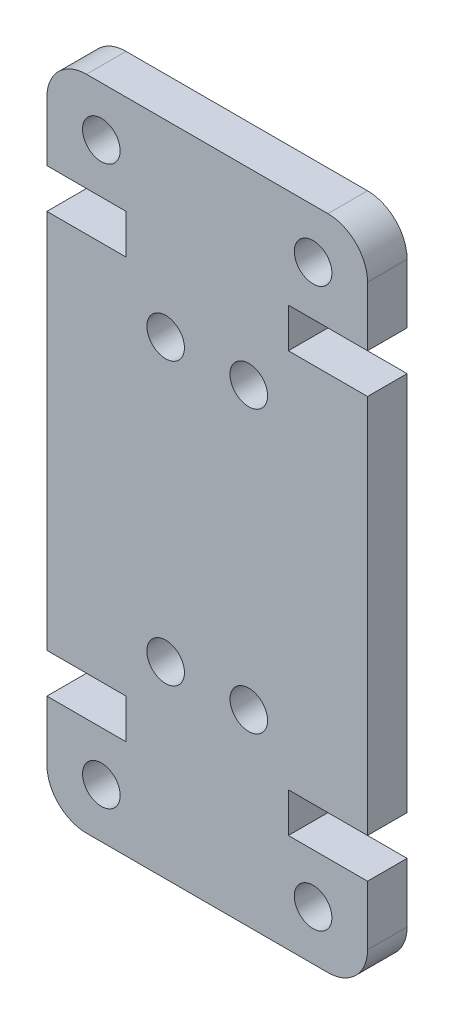
SolidWorks part; units mm, degrees
ref_plane "Front Plane" through (0, 0, 0) normal (0, 0, 1) x (1, 0, 0)
ref_plane "Top Plane" through (0, 0, 0) normal (0, 1, 0) x (1, 0, 0)
ref_plane "Right Plane" through (0, 0, 0) normal (1, 0, 0) x (0, 0, -1)
sketch "Sketch1" plane through (0, 0, 0) normal (0, 0, 1) x (1, 0, 0)
  line L0 (0, 26.21) -> (0, 7)
  line L1 (16.2, 2) -> (16.2, 5)
  line L2 (12.2, 5) -> (16.2, 5)
  line L3 (2, 0) -> (14.2, 0)
  line L4 (16.2, 7) -> (12.2, 7)
  line L5 (12.2, 7) -> (12.2, 5)
  line L6 (16.2, 26.21) -> (16.2, 7)
  line L7 (4, 7) -> (4, 5)
  line L8 (0, 31.21) -> (0, 28.21)
  line L9 (4, 28.21) -> (0, 28.21)
  line L10 (0, 7) -> (4, 7)
  line L11 (0, 26.21) -> (4, 26.21)
  line L12 (4, 5) -> (0, 5)
  line L13 (4, 26.21) -> (4, 28.21)
  line L14 (12.2, 26.21) -> (12.2, 28.21)
  line L15 (16.2, 26.21) -> (12.2, 26.21)
  line L16 (0, 2) -> (0, 5)
  line L17 (2, 33.21) -> (14.2, 33.21)
  line L18 (12.2, 28.21) -> (16.2, 28.21)
  line L19 (16.2, 31.21) -> (16.2, 28.21)
  line L20 (0, 16.605) -> (16.2, 16.605) construction
  line L21 (8.1, 33.21) -> (8.1, 0) construction
  circle A0 centre (13.45, 2.5) radius 0.95
  circle A1 centre (10.2, 9.5) radius 0.95
  arc A2 (16.2, 2) -> (14.2, 0) centre (14.2, 2) cw
  circle A3 centre (2.75, 30.71) radius 0.95
  circle A4 centre (6, 23.71) radius 0.95
  arc A5 (0, 2) -> (2, 0) centre (2, 2) ccw
  arc A6 (0, 31.21) -> (2, 33.21) centre (2, 31.21) cw
  circle A7 centre (6, 9.5) radius 0.95
  arc A8 (16.2, 31.21) -> (14.2, 33.21) centre (14.2, 31.21) ccw
  circle A9 centre (2.75, 2.5) radius 0.95
  circle A10 centre (10.2, 23.71) radius 0.95
  circle A11 centre (13.45, 30.71) radius 0.95
  point P15 (8.1, 16.605)
  dimension "D1" = 1.9
  dimension "D2" = 2
  dimension "D3" = 2.75
  dimension "D4" = 6
  dimension "D5" = 8.1
  dimension "D6" = 2.5
  dimension "D7" = 5
  dimension "D9" = 9.5
  dimension "D10" = 16.605
extrude "Boss-Extrude1" add sketch "Sketch1" along normal blind 4
sketch "Sketch2" plane through (0, 0, 0) normal (0, 0, 1) x (1, 0, 0)
  line L0 (0, 0) -> (16.2, 0)
  line L1 (16.2, 0) -> (16.2, 33.21)
  line L2 (16.2, 33.21) -> (0, 33.21)
  line L3 (0, 33.21) -> (0, 0)
extrude "Cut-Extrude2" cut sketch "Sketch2" along normal blind 2
